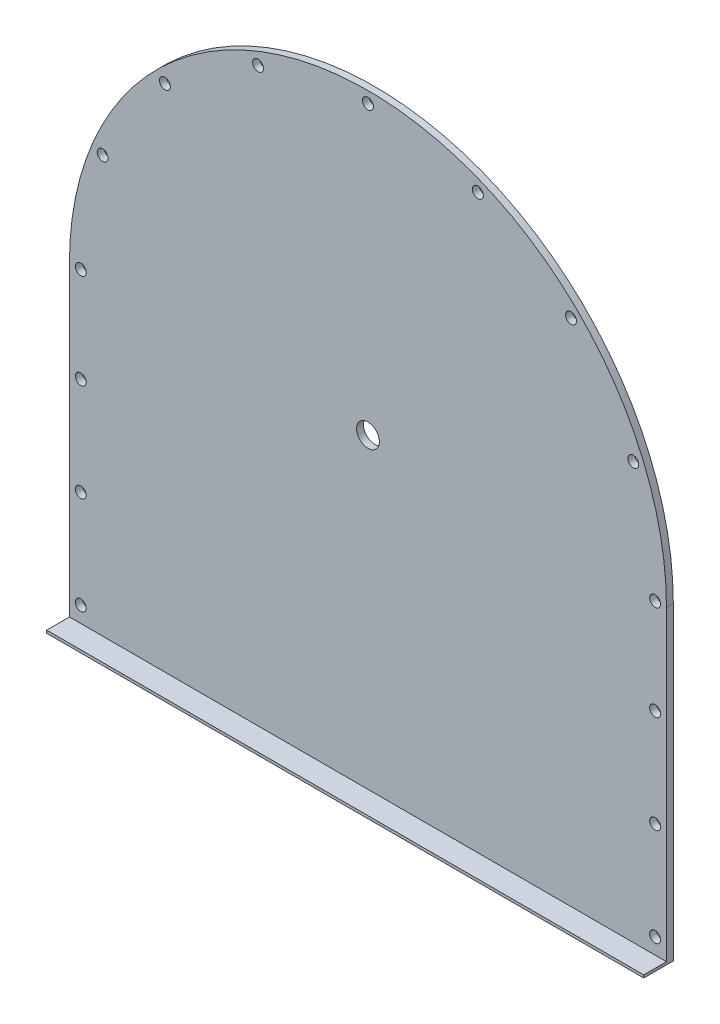
SolidWorks part; units mm, degrees
ref_plane "Front Plane" through (0, 0, 0) normal (0, 0, 1) x (1, 0, 0)
ref_plane "Top Plane" through (0, 0, 0) normal (0, 1, 0) x (1, 0, 0)
ref_plane "Right Plane" through (0, 0, 0) normal (1, 0, 0) x (0, 0, -1)
sketch "base plate" plane through (0, 0, 0) normal (0, 0, 1) x (1, 0, 0)
  line L1 (0, 0) -> (1312, 0)
  line L2 (0, 0) -> (0, 680)
  line L4 (1312, 0) -> (1312, 680)
  arc A0 (1312, 680) -> (0, 680) centre (656, 680) ccw
  dimension "D3" = 656
  dimension "D1" = 1312
  dimension "D2" = 680
extrude "Boss-Extrude1" add sketch "base plate" along normal blind 15
sketch "bottom flange" plane through (0, 0, 15) normal (0, 0, 1) x (1, 0, 0)
  line L0 (1312, 0) -> (1312, 680) construction
  line L1 (0, 0) -> (1312, 0)
  line L2 (0, 0) -> (0, 6)
  line L3 (0, 6) -> (1312, 6)
  line L4 (1312, 0) -> (1312, 6)
  dimension "D1" = 6
extrude "Boss-Extrude2" add sketch "bottom flange" along normal blind 50
sketch "Sketch5" plane through (0, 0, 15) normal (0, 0, 1) x (1, 0, 0)
  line L0 (1312, 680) -> (0, 680) construction
  line L1 (1312, 6) -> (1312, 680) construction
  line L2 (25, 680) -> (25, 6) construction
  line L3 (1312, 6) -> (0, 6) construction
  line L4 (1287, 680) -> (1287, 6) construction
  line L5 (25, 6) -> (25, 41) construction
  line L7 (25, 41) -> (25, 256) construction
  line L9 (25, 256) -> (25, 471) construction
  line L10 (656, 680) -> (656, 0) construction
  line L11 (0, 0) -> (1312, 0) construction
  arc A0 (1312, 680) -> (0, 680) centre (656, 680) ccw construction
  arc A1 (1287, 680) -> (25, 680) centre (656, 680) ccw construction
  point P10 (25, 680)
  point P11 (1287, 680)
  point P18 (25, 680)
  point P22 (1287, 680)
  point P27 (25, 41)
  point P32 (25, 256)
  point P37 (25, 471)
  point P50 (1287, 41)
  point P51 (1287, 256)
  point P52 (1287, 471)
  point P58 (25, 471)
  point P60 (25, 256)
  point P64 (25, 41)
  point P67 (1287, 680)
  point P80 (1238.968, 921.4732)
  point P81 (1102.1844, 1126.1844)
  point P82 (897.4732, 1262.968)
  point P83 (656, 1311)
  point P84 (414.5268, 1262.968)
  point P85 (209.8156, 1126.1844)
  point P86 (73.032, 921.4732)
  point P87 (25, 680)
  dimension "D1" = 631
  dimension "D2" = 35
  dimension "D3" = 215
  dimension "D4" = 215
  dimension "D5" = 9
hole_wizard "Ø24.0mm Dowel Hole1" positions "Sketch5" profile "Sketch6" hole size "Ø25.0" standard "ANSI Metric" end condition through all
sketch "Sketch6" plane through (25, 680, 15) normal (1, 0, 0) x (0, -1, 0)
  line L0 (0, 0) -> (0, 15)
  line L1 (0, 15) -> (12, 15)
  line L2 (12, 15) -> (12, 0)
  line L5 (12, 0) -> (0, 0)
  line L11 (0, -6.35) -> (0, 107.95) construction
  dimension "Thru Hole Dia." = 24
  dimension "Thru Hole Depth" = 15
sketch "center hole" plane through (0, 0, 15) normal (0, 0, 1) x (1, 0, 0)
  line L0 (0, 680) -> (1312, 680) construction
  circle A1 centre (656, 680) radius 25
  dimension "D1" = 50
extrude "Cut-Extrude1" cut sketch "center hole" against normal through all
